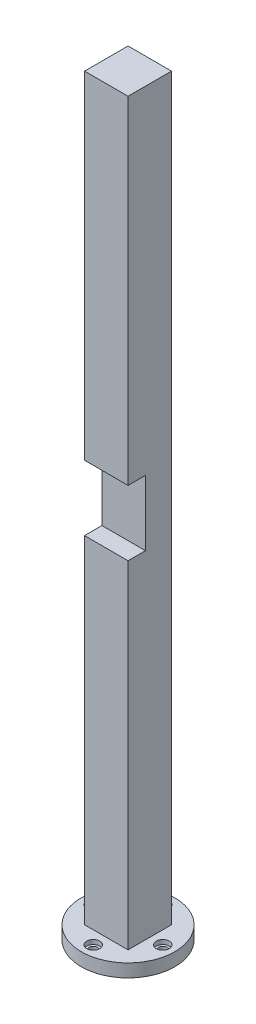
SolidWorks part; units mm, degrees
ref_plane "Front Plane" through (0, 0, 0) normal (0, 0, 1) x (1, 0, 0)
ref_plane "Top Plane" through (0, 0, 0) normal (0, 1, 0) x (1, 0, 0)
ref_plane "Right Plane" through (0, 0, 0) normal (1, 0, 0) x (0, 0, -1)
sketch "Sketch1" plane through (0, 0, 0) normal (0, 1, 0) x (1, 0, 0)
  line L1 (-5, -5) -> (5, -5)
  line L2 (-5, -5) -> (-5, 5)
  line L3 (-5, 5) -> (5, 5)
  line L4 (5, -5) -> (5, 5)
  line L5 (-5, -5) -> (5, 5) construction
  line L6 (-5, 5) -> (5, -5) construction
  point P0 (0, 0)
  dimension "D1" = 10
  dimension "D2" = 10
extrude "Boss-Extrude1" add sketch "Sketch1" along normal mid plane 170
sketch "Sketch2" plane through (0, 0, 5) normal (0, 0, 1) x (1, 0, 0)
  line L0 (5, 85) -> (5, -85) construction
  line L1 (-5, -7.5) -> (5, -7.5)
  line L2 (-5, -7.5) -> (-5, 7.5)
  line L3 (-5, 7.5) -> (5, 7.5)
  line L4 (5, -7.5) -> (5, 7.5)
  line L5 (-5, -7.5) -> (5, 7.5) construction
  line L6 (-5, 7.5) -> (5, -7.5) construction
  point P0 (0, 0)
  dimension "D1" = 15
extrude "Cut-Extrude1" cut sketch "Sketch2" against normal blind 4
sketch "Sketch3" plane through (0, -85, 0) normal (0, -1, 0) x (1, 0, 0)
  circle A0 centre (0, 0) radius 10.75
  dimension "D1" = 21.5
extrude "Boss-Extrude2" add sketch "Sketch3" along normal blind 3
sketch "Sketch4" plane through (0, -85, 0) normal (0, 1, 0) x (1, 0, 0)
  line L0 (0, 0) -> (8, 0) construction
  circle A0 centre (8, 0) radius 1
  circle A1 centre (0, -8) radius 1
  circle A2 centre (-8, 0) radius 1
  circle A3 centre (0, 8) radius 1
  point P13 (0, 0)
  dimension "D1" = 2
  dimension "D2" = 8
  dimension "D3" = 4
extrude "Cut-Extrude2" cut sketch "Sketch4" against normal blind 3
sketch "Sketch5" plane through (0, -85, 0) normal (0, 1, 0) x (1, 0, 0)
  circle A0 centre (8, 0) radius 1.5
  circle A1 centre (0, -8) radius 1.5
  circle A2 centre (-8, 0) radius 1.5
  circle A3 centre (0, 8) radius 1.5
  point P12 (0, 0)
  dimension "D1" = 3
  dimension "D2" = 4
extrude "Cut-Extrude3" cut sketch "Sketch5" against normal blind 1
